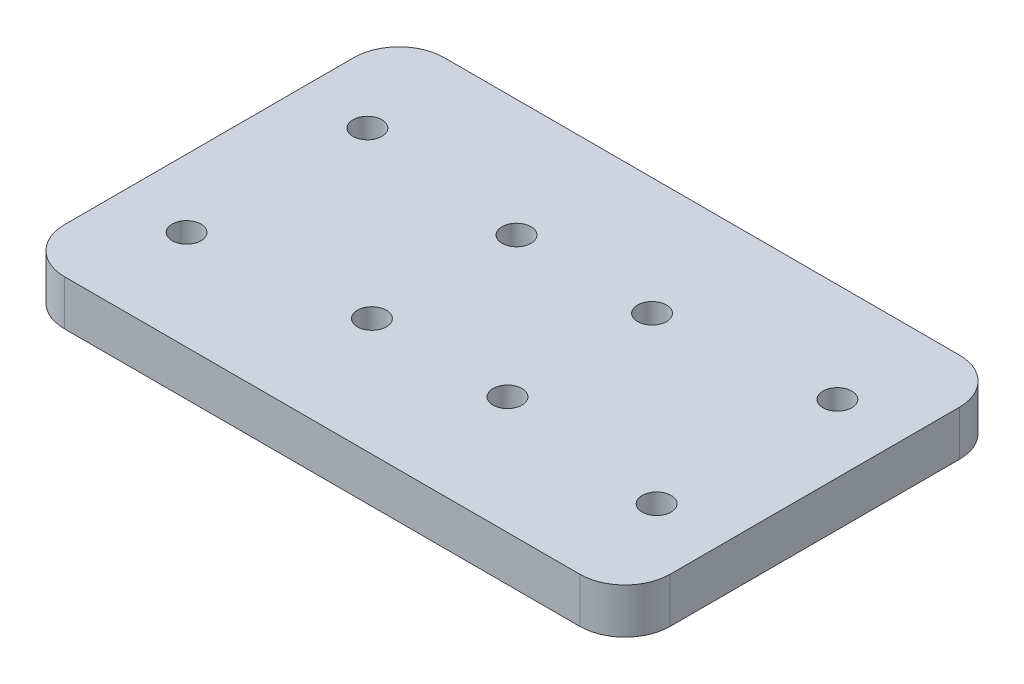
SolidWorks part; units mm, degrees
material "Acrylic (Medium-high impact)"
ref_plane "Front Plane" through (0, 0, 0) normal (0, 0, 1) x (1, 0, 0)
ref_plane "Top Plane" through (0, 0, 0) normal (0, 1, 0) x (1, 0, 0)
ref_plane "Right Plane" through (0, 0, 0) normal (1, 0, 0) x (0, 0, -1)
sketch "Sketch1" plane through (0, 0, 0) normal (0, 1, 0) x (1, 0, 0)
  line L0 (7.5, 42) -> (7.5, 0) construction
  line L1 (0, 0) -> (67, 0)
  line L2 (0, 0) -> (0, 42)
  line L3 (0, 42) -> (67, 42)
  line L4 (67, 0) -> (67, 42)
  line L5 (33.5, 42) -> (33.5, 0) construction
  line L6 (67, 21) -> (0, 21) construction
  circle A0 centre (7.5, 31) radius 1.6
  circle A1 centre (7.5, 11) radius 1.6
  circle A2 centre (59.5, 11) radius 1.6
  circle A3 centre (59.5, 31) radius 1.6
  dimension "D3" = 20
  dimension "D4" = 3.2
  dimension "D1" = 67
  dimension "D2" = 42
  dimension "D5" = 7.5
extrude "Boss-Extrude1" add sketch "Sketch1" along normal blind 5
sketch "Sketch2" plane through (0, 5, 0) normal (0, 1, 0) x (1, 0, 0)
  line L0 (33.5, 29) -> (33.5, 13) construction
  line L1 (26, 13) -> (41, 13) construction
  line L2 (26, 13) -> (26, 29) construction
  line L3 (26, 29) -> (41, 29) construction
  line L4 (41, 13) -> (41, 29) construction
  line L5 (0, 21) -> (67, 21) construction
  line L6 (0, 42) -> (0, 0) construction
  line L7 (67, 0) -> (67, 42) construction
  circle A0 centre (41, 29) radius 1.6
  circle A1 centre (41, 13) radius 1.6
  circle A2 centre (26, 13) radius 1.6
  circle A3 centre (26, 29) radius 1.6
  point P12 (33.5, 21)
  dimension "D1" = 3.2
  dimension "D2" = 16
  dimension "D3" = 15
extrude "Cut-Extrude1" cut sketch "Sketch2" against normal through all
fillet "Fillet1" radius 5 4 edges at (0, 2.5, -42) (67, 2.5, -42) (67, 2.5, 0) (0, 2.5, 0)
